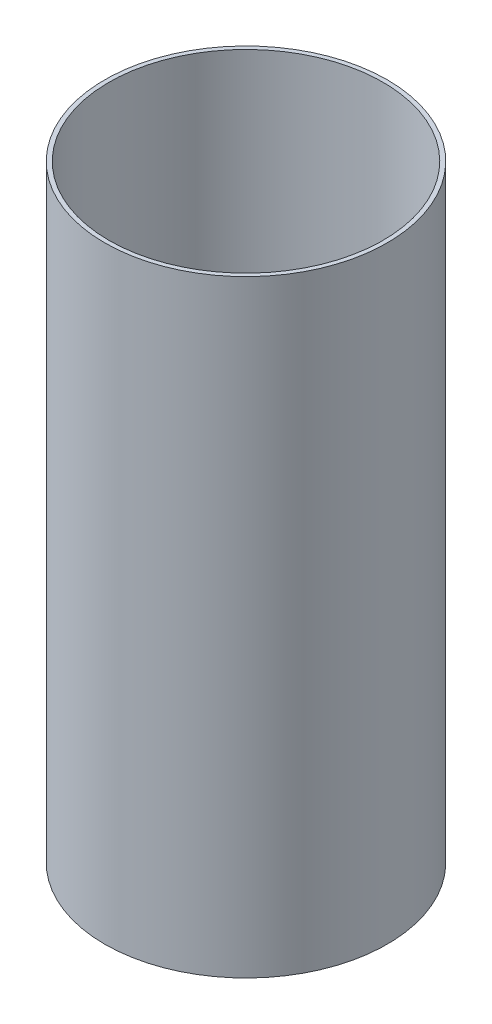
SolidWorks part; units mm, degrees
ref_plane "Front Plane" through (0, 0, 0) normal (0, 0, 1) x (1, 0, 0)
ref_plane "Top Plane" through (0, 0, 0) normal (0, 1, 0) x (1, 0, 0)
ref_plane "Right Plane" through (0, 0, 0) normal (1, 0, 0) x (0, 0, -1)
sketch "Sketch1" plane through (0, 0, 0) normal (0, 1, 0) x (1, 0, 0)
  circle A0 centre (0, 0) radius 63.5
  circle A1 centre (0, 0) radius 61.595
  dimension "D1" = 127
  dimension "D2" = 123.19
extrude "Boss-Extrude1" add sketch "Sketch1" along normal mid plane 273.05
